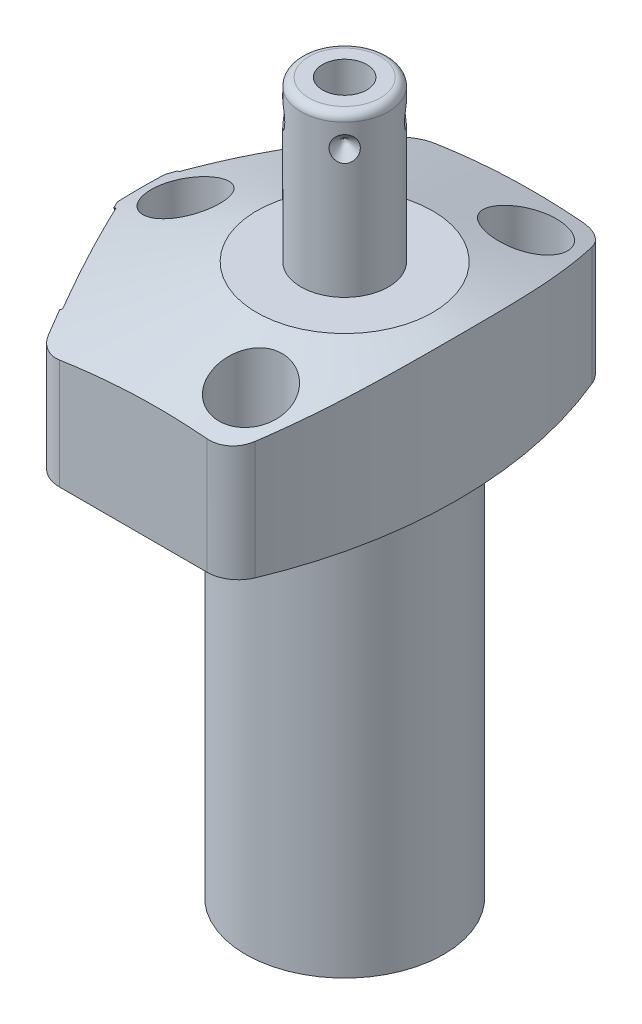
SolidWorks part; units mm, degrees
material "Alloy Steel"
ref_plane "Front Plane" through (0, 0, 0) normal (0, 0, 1) x (1, 0, 0)
ref_plane "Top Plane" through (0, 0, 0) normal (0, 1, 0) x (1, 0, 0)
ref_plane "Right Plane" through (0, 0, 0) normal (1, 0, 0) x (0, 0, -1)
ref_plane "Plane1" through (0, 0, 0) normal (0, 0, 1) x (0, -1, 0)
sketch "Sketch1" plane through (0, 0, 0) normal (0, 0, 1) x (0, -1, 0)
  line L0 (0, 28.575) -> (-19.05, 28.575)
  line L1 (-19.05, 28.575) -> (-19.05, 0)
  line L2 (-19.05, 0) -> (50.8, 0)
  line L3 (50.8, 0) -> (50.8, 12.573)
  line L4 (50.8, 12.573) -> (0, 12.573)
  line L5 (0, 12.573) -> (0, 28.575)
  line L6 (-22.5425, 0) -> (54.2925, 0) construction
  dimension "D1" = 69.85
  dimension "D2" = 19.05
  dimension "D3" = 25.146
  dimension "D4" = 57.15
revolve "Revolve1" add sketch "Sketch1" angle 360 about L6
ref_plane "Plane2" through (0, 0, 0) normal (0, -1, 0) x (0, 0, -1)
sketch "Sketch2" plane through (0, 0, 0) normal (0, -1, 0) x (0, 0, -1)
  line L0 (23.8125, -15.7954) -> (23.8125, 15.7954)
  line L2 (-23.8125, 15.7954) -> (-23.8125, -15.7954)
  line L3 (0, -18.0139) -> (0, 30.7935) construction
  arc A0 (23.8125, -15.7954) -> (23.8125, 15.7954) centre (0, 0) ccw
  circle A1 centre (0, 0) radius 28.575
  arc A2 (-23.8125, 15.7954) -> (-23.8125, -15.7954) centre (0, 0) ccw
  point P4 (0, 0)
  dimension "D1" = 47.625
  dimension "D2" = 0
extrude "Cut-Extrude1" cut sketch "Sketch2" against normal up to next
ref_plane "Plane3" through (0, 0, 0) normal (0, -1, 0) x (-1, 0, 0)
sketch "Sketch3" plane through (0, 0, 0) normal (0, -1, 0) x (-1, 0, 0)
  line L0 (14.7539, 23.8125) -> (27.4152, 0)
  line L1 (27.4152, 0) -> (14.7539, -23.8125)
  line L2 (-24.5787, -13.0687) -> (45.9515, 24.4329) construction
  line L3 (0, 0) -> (35.175, 0) construction
  line L4 (15.7954, -23.8125) -> (-15.7954, -23.8125) construction
  line L5 (-15.7954, 23.8125) -> (15.7954, 23.8125) construction
  line L6 (15.7954, -23.8125) -> (14.7539, -23.8125)
  line L7 (14.7539, 23.8125) -> (15.7954, 23.8125)
  arc A0 (15.7954, -23.8125) -> (15.7954, 23.8125) centre (0, 0) ccw construction
  arc A1 (15.7954, -23.8125) -> (15.7954, 23.8125) centre (0, 0) ccw
  dimension "D1" = 28
  dimension "D2" = 24.2062
extrude "Cut-Extrude2" cut sketch "Sketch3" against normal up to next
ref_plane "Plane4" through (0, 0, 0) normal (0, -1, 0) x (-1, 0, 0)
sketch "S2D0002" plane through (0, 0, 0) normal (0, -1, 0) x (-1, 0, 0)
  line L0 (25.8064, 53.3791) -> (25.8064, -53.3791)
  arc A0 (25.8064, 53.3791) -> (25.8064, -53.3791) centre (41.275, 0) ccw
  dimension "D1" = 55.5752
  dimension "D2" = 15.4686
  dimension "D3" = 41.275
extrude "Cut-Extrude3" cut sketch "S2D0002" against normal blind 26.035 flip side to cut
fillet "Fillet1" radius 3.9624 4 edges at (8.9402, 9.525, 23.8125) (-14.7539, 9.525, 23.8125) (-14.7539, 9.525, -23.8125) (8.9402, 9.525, -23.8125)
ref_plane "Plane5" through (0, 0, 0) normal (0, 0, 1) x (1, 0, 0)
sketch "Sketch5" plane through (0, 0, 0) normal (0, 0, 1) x (1, 0, 0)
  line L0 (-11.176, 19.05) -> (-44.45, 8.2386)
  line L1 (0, 5.9984) -> (0, 19.6715) construction
  line L2 (-15.8716, 19.05) -> (-25.8064, 19.05) construction
  line L3 (-11.176, 19.05) -> (-44.45, 19.05)
  line L4 (-44.45, 19.05) -> (-44.45, 8.2386)
  dimension "D1" = 22.352
  dimension "D2" = 18
  dimension "D3" = 44.45
revolve "Cut-Revolve1" cut sketch "Sketch5" angle 360 about L1
ref_plane "Plane6" through (-21.1485, 7.9502, -11.2449) normal (0, 1, 0) x (0.4695, 0, -0.8829)
sketch "Sketch6" plane through (-21.1485, 7.9502, -11.2449) normal (0, 1, 0) x (0.4695, 0, -0.8829)
  line L0 (0, 0) -> (4.5466, 0)
  line L1 (4.5466, 0) -> (4.1066, -2.0701)
  line L2 (4.1066, -2.0701) -> (3.4544, -2.7223)
  line L3 (3.4544, -2.7223) -> (3.4544, -12.192)
  line L4 (3.4544, -12.192) -> (0, -12.192)
  line L5 (0, -12.192) -> (0, 0)
  line L6 (0, -12.8016) -> (0, 0.6096) construction
  dimension "D1" = 12.192
revolve "Cut-Revolve2" cut sketch "Sketch6" angle 360 about L6
ref_plane "Plane7" through (-21.1485, 7.9502, 11.2449) normal (0, 1, 0) x (-0.4695, 0, -0.8829)
sketch "Sketch7" plane through (-21.1485, 7.9502, 11.2449) normal (0, 1, 0) x (-0.4695, 0, -0.8829)
  line L0 (0, 0) -> (4.5466, 0)
  line L1 (4.5466, 0) -> (4.1066, -2.0701)
  line L2 (4.1066, -2.0701) -> (3.4544, -2.7223)
  line L3 (3.4544, -2.7223) -> (3.4544, -12.192)
  line L4 (3.4544, -12.192) -> (0, -12.192)
  line L5 (0, -12.192) -> (0, 0)
  line L6 (0, -12.8016) -> (0, 0.6096) construction
  dimension "D1" = 12.192
revolve "Cut-Revolve3" cut sketch "Sketch7" angle 360 about L6
ref_plane "Plane8" through (-11.1252, 2.667, -15.875) normal (0, 0, 1) x (-1, 0, 0)
sketch "Sketch17" plane through (-21.3728, 0, 11.3641) normal (-0.8829, 0, 0.4695) x (0.4695, 0, 0.8829)
  circle A0 centre (0, 7.9502) radius 10.4775
  dimension "D1" = 20.955
extrude "Cut-Extrude4" cut sketch "Sketch17" against normal blind 0.254
sketch "Sketch18" plane through (-21.3728, 0, -11.3641) normal (-0.8829, 0, -0.4695) x (-0.4695, 0, 0.8829)
  circle A0 centre (0, 7.9502) radius 10.4775
  dimension "D1" = 20.955
extrude "Cut-Extrude5" cut sketch "Sketch18" against normal blind 0.254
sketch "Sketch8" plane through (-11.1252, 2.667, -15.875) normal (0, 0, 1) x (-1, 0, 0)
  line L0 (0, 0) -> (4.5466, 0)
  line L1 (4.5466, 0) -> (4.1066, -2.0701)
  line L2 (4.1066, -2.0701) -> (3.4544, -2.7223)
  line L3 (3.4544, -2.7223) -> (3.4544, -11.684)
  line L4 (3.4544, -11.684) -> (0, -11.684)
  line L5 (0, -11.684) -> (0, 0)
  line L6 (0, -12.2682) -> (0, 0.5842) construction
  dimension "D1" = 11.684
revolve "Cut-Revolve4" cut sketch "Sketch8" angle 360 about L6
ref_plane "Plane9" through (-11.1252, 2.667, 15.875) normal (0, 0, 1) x (-1, 0, 0)
sketch "Sketch9" plane through (-11.1252, 2.667, 15.875) normal (0, 0, 1) x (-1, 0, 0)
  line L0 (0, 0) -> (4.5466, 0)
  line L1 (4.5466, 0) -> (4.1066, -2.0701)
  line L2 (4.1066, -2.0701) -> (3.4544, -2.7223)
  line L3 (3.4544, -2.7223) -> (3.4544, -11.684)
  line L4 (3.4544, -11.684) -> (0, -11.684)
  line L5 (0, -11.684) -> (0, 0)
  line L6 (0, -12.2682) -> (0, 0.5842) construction
  dimension "D1" = 11.684
revolve "Cut-Revolve5" cut sketch "Sketch9" angle 360 about L6
ref_plane "Plane10" through (0, 0, 0) normal (1, 0, 0) x (0, 0, -1)
sketch "Sketch10" plane through (0, 0, 0) normal (1, 0, 0) x (0, 0, -1)
  line L0 (0, 19.05) -> (-5.5562, 19.05)
  line L1 (-5.5562, 19.05) -> (-5.5562, 38.3032)
  line L2 (-4.5402, 39.3192) -> (0, 39.3192)
  line L3 (0, 39.3192) -> (0, 19.05)
  line L4 (0, 18.0365) -> (0, 44.824) construction
  line L5 (11.176, 19.05) -> (-11.176, 19.05) construction
  line L6 (-21.374, 0) -> (21.374, 0) construction
  arc A0 (-4.5402, 39.3192) -> (-5.5562, 38.3032) centre (-4.5402, 38.3032) ccw
  dimension "D3" = 1.016
  dimension "D1" = 11.1125
  dimension "D2" = 39.3192
revolve "Revolve2" add sketch "Sketch10" angle 360 about L4
sketch "Sketch19" plane through (0, 0, 0) normal (0, -1, 0) x (1, 0, 0)
  circle A0 centre (-11.1252, -15.875) radius 5.5626
  circle A1 centre (-11.1252, 15.875) radius 5.5626
  dimension "D1" = 11.1252
extrude "Cut-Extrude6" cut sketch "Sketch19" against normal blind 2.667
ref_plane "Plane11" through (2.8067, 39.3192, 0) normal (0, 0, 1) x (1, 0, 0)
sketch "S2D0001" plane through (2.8067, 39.3192, 0) normal (0, 0, 1) x (1, 0, 0)
  line L0 (0, 0) -> (0, -10.16)
  line L1 (0, -10.16) -> (-2.8067, -11.8464)
  line L2 (0, 0) -> (-2.8067, 0)
  line L3 (-2.8067, 0) -> (-2.8067, -11.8464)
  line L4 (-2.8067, -17.5667) -> (-2.8067, 0.5923) construction
  line L5 (1.7335, 0) -> (-7.3469, 0) construction
  dimension "D1" = 5.6134
  dimension "D2" = 10.16
  dimension "D3" = 59
revolve "Cut-Revolve6" cut sketch "S2D0001" angle 360 about L4
ref_plane "Plane12" through (-21.1485, 0, -11.2449) normal (0.8829, 0, 0.4695) x (0.4695, 0, -0.8829)
sketch "Sketch12" plane through (-21.1485, 0, -11.2449) normal (0.8829, 0, 0.4695) x (0.4695, 0, -0.8829)
  circle A0 centre (0, 7.9502) radius 4.8006
  circle A1 centre (0, 7.9502) radius 3.4544 construction
  dimension "D1" = 9.6012
extrude "Extrude1" add sketch "Sketch12" against normal blind 1.651
sketch "Sketch13" plane through (0, 0, 0) normal (0, -1, 0) x (1, 0, 0)
  circle A0 centre (-11.1252, -15.875) radius 4.8006
  circle A1 centre (-11.1252, -15.875) radius 5.5626 construction
  dimension "D1" = 9.6012
ref_plane "Plane13" through (-11.1252, 2.667, -15.875) normal (0, 1, 0) x (-1, 0, 0)
extrude "Extrude2" add sketch "Sketch13" against normal up to surface
ref_plane "Plane14" through (-11.1252, 0, 15.875) normal (1, 0, 0) x (0, 0, -1)
sketch "Sketch14" plane through (-11.1252, 0, 15.875) normal (1, 0, 0) x (0, 0, -1)
  line L0 (5.461, 2.667) -> (5.461, 0.9398)
  line L1 (5.461, 0.9398) -> (5.3016, 0.9398)
  line L2 (2.667, 0.4318) -> (2.667, 0.127)
  line L3 (2.667, 0.127) -> (1.5875, 0.127)
  line L4 (1.5875, 0.127) -> (1.5875, 10.6172)
  line L5 (1.5875, 10.6172) -> (3.2512, 10.6172)
  line L6 (3.2512, 10.6172) -> (3.2512, 2.667)
  line L7 (3.2512, 2.667) -> (5.461, 2.667)
  line L8 (3.175, 0.9398) -> (3.8424, 0.9398)
  line L9 (0, -1.0109) -> (0, 11.1709) construction
  line L10 (-3.4544, 14.351) -> (-3.4544, 5.3893) construction
  line L11 (3.4544, 5.3893) -> (3.4544, 14.351) construction
  line L12 (-5.499, 0) -> (37.249, 0) construction
  arc A0 (3.175, 0.9398) -> (2.667, 0.4318) centre (3.175, 0.4318) ccw
  arc A1 (3.8424, 0.9398) -> (5.3016, 0.9398) centre (4.572, 0.4318) ccw
  dimension "D5" = 0.508
  dimension "D9" = 0.889
  dimension "D1" = 2.54
  dimension "D2" = 7.9502
  dimension "D3" = 3.175
  dimension "D4" = 0.127
  dimension "D6" = 5.334
  dimension "D7" = 0.3048
  dimension "D8" = 0.3048
  dimension "D10" = 9.144
  dimension "D11" = 10.922
  dimension "D12" = 6.5024
revolve "Revolve3" add sketch "Sketch14" angle 360 about L9
ref_plane "Plane15" through (-5.5562, 35.3568, 0) normal (0, 0, 1) x (0, 1, 0)
ref_plane "Plane17" through (0, 0, 0) normal (-0.7071, 0, 0.7071) x (0.7071, 0, 0.7071)
sketch "Sketch15" plane through (-3.9289, 35.3568, -3.9289) normal (-0.7071, 0, 0.7071) x (0, 1, 0)
  line L0 (0, 0) -> (1.5875, 0)
  line L1 (1.5875, 0) -> (0, -1.5875)
  line L2 (0, 0) -> (0, -1.5875)
  line L3 (0, -3.7018) -> (0, 0.0794) construction
  line L4 (2.9464, 0) -> (-16.3068, 0) construction
  line L5 (3.9624, -10.0965) -> (3.9624, -1.016) construction
  dimension "D1" = 3.9624
  dimension "D2" = 3.175
  dimension "D3" = 45
ref_plane "Plane16" through (5.5562, 35.3568, 0) normal (0, 0, 1) x (0, -1, 0)
revolve "Cut-Revolve7" cut sketch "Sketch15" angle 360 about L3
pattern_circular "CirPattern1" count 4 over 360 about axis through (0, 18.0365, 0) along (0, -1, 0) of "Cut-Revolve7"
hole_wizard "Hole1" positions "Sketch21" profile "Sketch20" legacy end condition up to next
sketch "Sketch21" plane through (0, 19.05, 0) normal (0, 1, 0) x (-1, 0, 0)
  line L0 (0, 0) -> (31.1465, 0) construction
  line L1 (0, 0) -> (0, 26.4037) construction
  point P0 (-5.5626, -17.4498)
  point P9 (20.193, 0)
  point P13 (-5.5626, 17.4498)
  dimension "D1" = 5.5626
  dimension "D2" = 17.4498
  dimension "D3" = 20.193
sketch "Sketch20" plane through (5.5626, 19.05, -17.4498) normal (1, 0, 0) x (0, 0, 1)
  line L0 (0, 0) -> (0, 19.05)
  line L1 (0, 19.05) -> (2.7813, 19.05)
  line L2 (2.7813, 19.05) -> (2.7813, 11.0998)
  line L3 (2.7813, 11.0998) -> (4.3561, 11.0998)
  line L4 (4.3561, 11.0998) -> (4.3561, 0)
  line L5 (4.3561, 0) -> (0, 0)
  line L6 (0, 110) -> (0, -10) construction
  dimension "Diameter" = 5.5626
  dimension "Depth" = 19.05
  dimension "C-Bore Diameter" = 8.7122
  dimension "C-Bore Depth" = 11.0998
